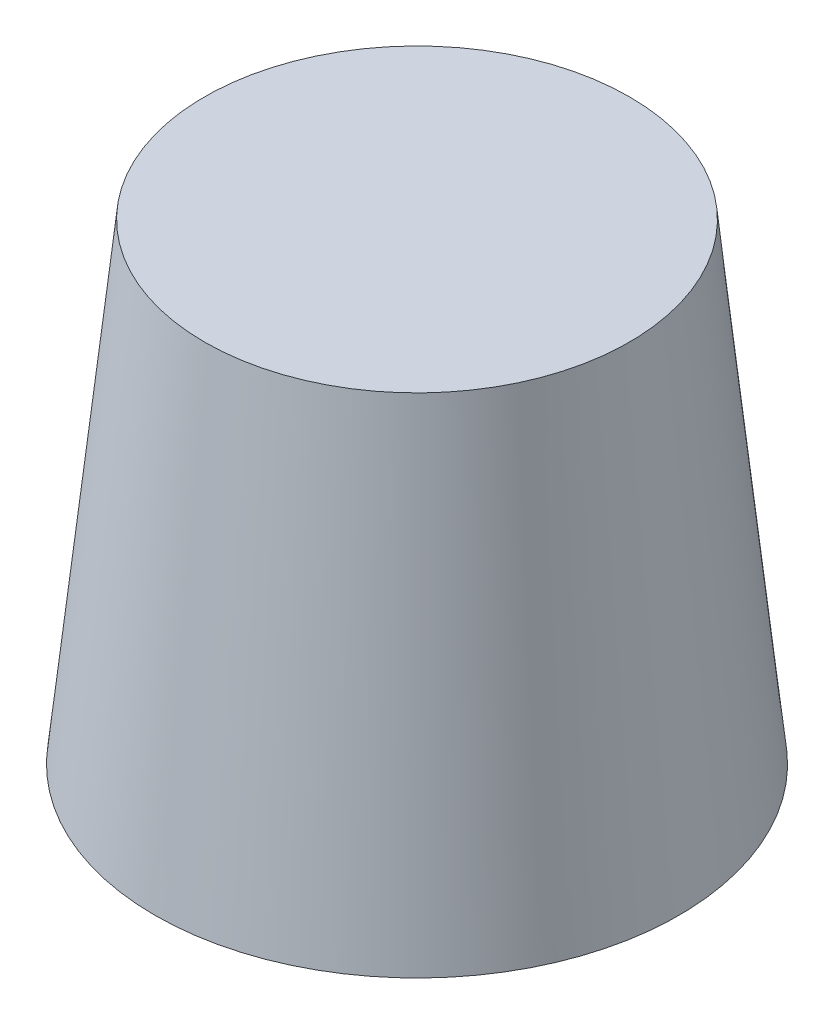
SolidWorks part; units mm, degrees
ref_plane "Plan de face" through (0, 0, 0) normal (0, 0, 1) x (1, 0, 0)
ref_plane "Plan de dessus" through (0, 0, 0) normal (0, 1, 0) x (1, 0, 0)
ref_plane "Plan de droite" through (0, 0, 0) normal (1, 0, 0) x (0, 0, -1)
sketch "Esquisse2" plane through (0, 0, 0) normal (0, 1, 0) x (1, 0, 0)
  circle A0 centre (0, 0) radius 5
  dimension "D1" = 10
extrude "Boss.-Extru.1" add sketch "Esquisse2" along normal blind 9 draft 6
sketch "Esquisse3" plane through (0, 0, 0) normal (0, -1, 0) x (1, 0, 0)
  line L0 (-1.2, -2.7) -> (1.2, 2.7) construction
  line L1 (-1.2, -2.7) -> (1.2, -2.7)
  line L2 (-1.2, -2.7) -> (-1.2, 2.7)
  line L3 (-1.2, 2.7) -> (1.2, 2.7)
  line L4 (1.2, -2.7) -> (1.2, 2.7)
  point P4 (0, 0)
  dimension "D1" = 2.4
  dimension "D2" = 5.4
extrude "Enlèv. mat.-Extru.1" cut sketch "Esquisse3" against normal blind 7
